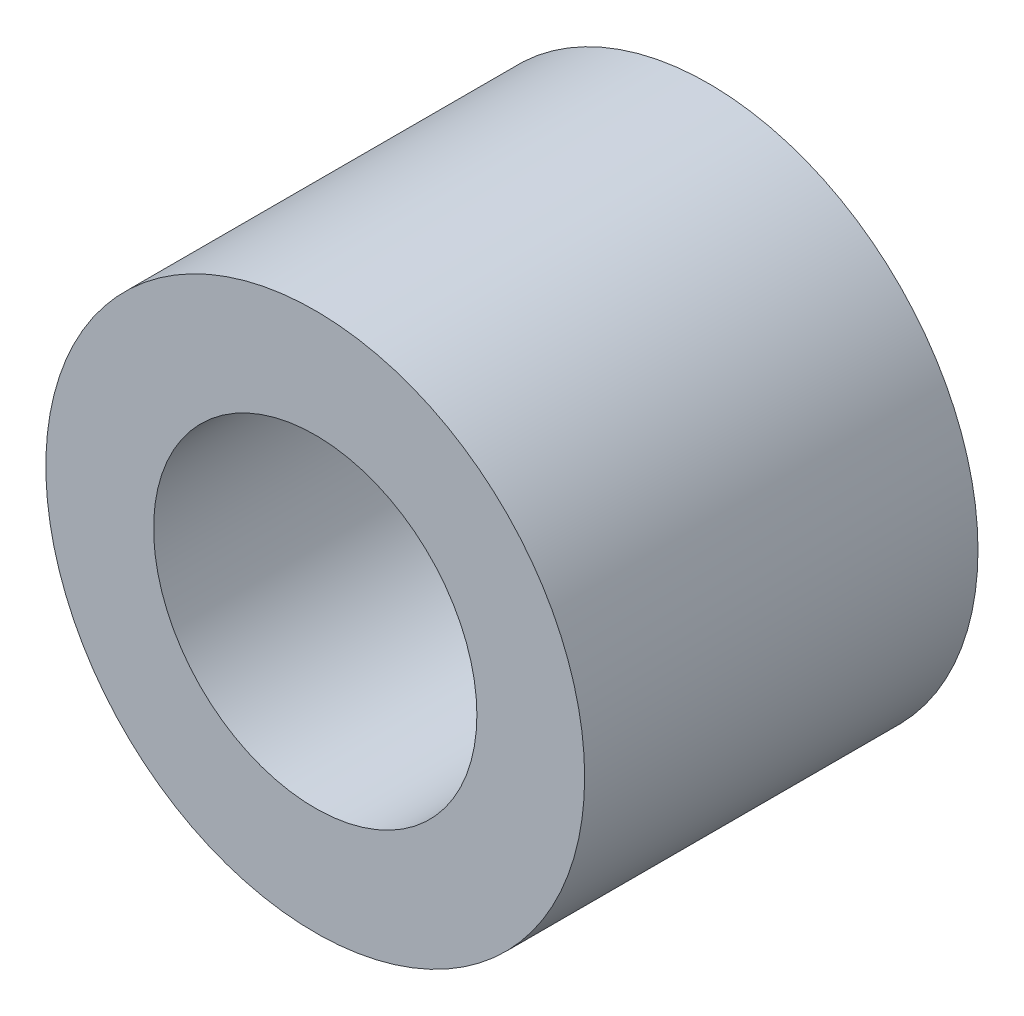
SolidWorks part; units mm, degrees
material "ﾎﾟﾘｵｷｼﾒﾁﾚﾝ(POM)ｱｾﾀｰﾙ共重合体"
ref_plane "Front Plane" through (0, 0, 0) normal (0, 0, 1) x (1, 0, 0)
ref_plane "Top Plane" through (0, 0, 0) normal (0, 1, 0) x (1, 0, 0)
ref_plane "Right Plane" through (0, 0, 0) normal (1, 0, 0) x (0, 0, -1)
sketch "Sketch2" plane through (0, 0, 0) normal (0, 0, 1) x (1, 0, 0)
  circle A0 centre (0, 0) radius 2.5
  circle A1 centre (0, 0) radius 1.5
  dimension "D1" = 3
  dimension "D2" = 5
  dimension "D3" = 5
extrude "Boss-Extrude1" add sketch "Sketch2" along normal blind 3.65
